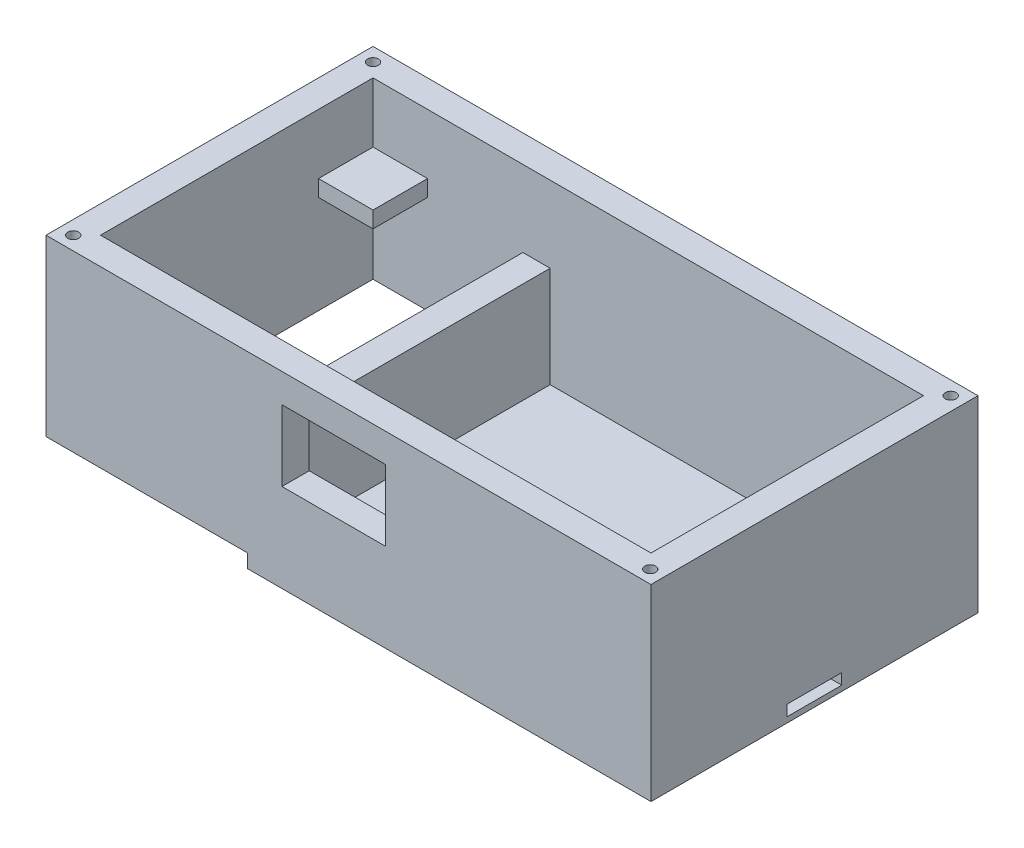
SolidWorks part; units mm, degrees
ref_plane "Front Plane" through (0, 0, 0) normal (0, 0, 1) x (1, 0, 0)
ref_plane "Top Plane" through (0, 0, 0) normal (0, 1, 0) x (1, 0, 0)
ref_plane "Right Plane" through (0, 0, 0) normal (1, 0, 0) x (0, 0, -1)
sketch "Sketch1" plane through (0, 0, 0) normal (0, 1, 0) x (1, 0, 0)
  line L1 (0, 0) -> (111, 0)
  line L2 (0, 0) -> (0, 60)
  line L3 (0, 60) -> (111, 60)
  line L4 (111, 0) -> (111, 60)
  dimension "D1" = 111
  dimension "D2" = 60
extrude "Boss-Extrude1" add sketch "Sketch1" along normal blind 34.5
sketch "Sketch2" plane through (0, 34.5, 0) normal (0, 1, 0) x (1, 0, 0)
  line L0 (55.5, 60) -> (55.5, 0) construction
  line L1 (111, 60) -> (0, 60) construction
  line L2 (0, 0) -> (111, 0) construction
  line L3 (0, 30) -> (111, 30) construction
  line L4 (0, 60) -> (0, 0) construction
  line L5 (111, 0) -> (111, 60) construction
  line L7 (5, 5) -> (106, 5)
  line L8 (5, 5) -> (5, 55)
  line L9 (5, 55) -> (106, 55)
  line L10 (106, 5) -> (106, 55)
  dimension "D1" = 5
  dimension "D2" = 5
  dimension "D3" = 5
  dimension "D4" = 5
  dimension "D5" = 50
  dimension "D6" = 101
extrude "Cut-Extrude1" cut sketch "Sketch2" against normal blind 11
sketch "Sketch3" plane through (0, 34.5, 0) normal (0, 1, 0) x (1, 0, 0)
  line L0 (5, 45) -> (15, 45)
  line L1 (5, 55) -> (5, 5) construction
  line L2 (15, 45) -> (15, 55)
  line L3 (106, 55) -> (5, 55) construction
  line L4 (15, 55) -> (96, 55)
  line L5 (96, 55) -> (96, 45)
  line L6 (96, 45) -> (106, 45)
  line L7 (106, 5) -> (106, 55) construction
  line L8 (106, 45) -> (106, 15)
  line L9 (106, 5) -> (106, 55) construction
  line L10 (106, 15) -> (96, 15)
  line L11 (96, 15) -> (96, 5)
  line L12 (5, 5) -> (106, 5) construction
  line L13 (96, 5) -> (15, 5)
  line L14 (15, 5) -> (15, 15)
  line L15 (15, 15) -> (5, 15)
  line L16 (5, 55) -> (5, 5) construction
  line L17 (5, 15) -> (5, 45)
  dimension "D1" = 10
  dimension "D2" = 10
  dimension "D3" = 10
  dimension "D4" = 10
  dimension "D5" = 10
  dimension "D6" = 10
  dimension "D7" = 10
  dimension "D8" = 10
extrude "Cut-Extrude3" cut sketch "Sketch3" against normal blind 14
sketch "Sketch5" plane through (0, 0, 0) normal (0, -1, 0) x (1, 0, 0)
  line L1 (5, -5) -> (32.5, -5)
  line L2 (5, -5) -> (5, -55)
  line L3 (5, -55) -> (32.5, -55)
  line L4 (32.5, -5) -> (32.5, -55)
  line L6 (0, 0) -> (111, 0) construction
  line L7 (0, -60) -> (0, 0) construction
  line L14 (111, 0) -> (111, -60) construction
  line L15 (106, -55) -> (37.5, -55)
  line L16 (106, -55) -> (106, -5)
  line L17 (106, -5) -> (37.5, -5)
  line L18 (37.5, -55) -> (37.5, -5)
  line L19 (111, -60) -> (0, -60) construction
  dimension "D1" = 27.5
  dimension "D2" = 50
  dimension "D3" = 5
  dimension "D4" = 5
  dimension "D5" = 5
  dimension "D6" = 5
  dimension "D7" = 5
  dimension "D8" = 5
  dimension "D9" = 5
extrude "Cut-Extrude5" cut sketch "Sketch5" against normal blind 18.5 from offset 2 offset against normal yes
sketch "Sketch6" plane through (0, 0, 0) normal (0, -1, 0) x (1, 0, 0)
  line L0 (0, 0) -> (111, 0) construction
  line L1 (0, -60) -> (37, -60)
  line L2 (0, -60) -> (0, 0)
  line L3 (0, 0) -> (37, 0)
  line L4 (37, -60) -> (37, 0)
  dimension "D1" = 60
  dimension "D2" = 37
extrude "Cut-Extrude6" cut sketch "Sketch6" against normal blind 2.5
sketch "Sketch7" plane through (0, 2.5, 0) normal (0, -1, 0) x (-1, 0, 0)
  line L0 (-37, 0) -> (0, 0) construction
  line L1 (0, 0) -> (0, 60) construction
  line L2 (0, 60) -> (-37, 60) construction
  line L3 (-37, 60) -> (-37, 0) construction
  line L4 (-37, 60) -> (-37, 0) construction
  circle A0 centre (-2.5, 57.5) radius 1
  circle A1 centre (-34.5, 57.5) radius 1
  circle A2 centre (-34.5, 2.5) radius 1
  circle A3 centre (-2.5, 2.5) radius 1
  dimension "D1" = 2
  dimension "D2" = 2
  dimension "D3" = 2
  dimension "D4" = 2
  dimension "D5" = 2.5
  dimension "D6" = 2.5
  dimension "D7" = 2.5
  dimension "D8" = 2.5
  dimension "D9" = 2.5
  dimension "D10" = 2.5
  dimension "D11" = 2.5
  dimension "D12" = 2.5
extrude "Cut-Extrude7" cut sketch "Sketch7" against normal blind 4
sketch "Sketch8" plane through (0, 34.5, 0) normal (0, 1, 0) x (1, 0, 0)
  line L0 (111, 60) -> (0, 60) construction
  line L1 (111, 0) -> (111, 60) construction
  line L2 (0, 60) -> (0, 0) construction
  line L3 (0, 0) -> (111, 0) construction
  circle A0 centre (2.5, 57.5) radius 1
  circle A1 centre (108.5, 57.5) radius 1
  circle A2 centre (108.5, 2.3604) radius 1
  circle A3 centre (2.5, 2.5) radius 1
  dimension "D8" = 2
  dimension "D9" = 2
  dimension "D10" = 2
  dimension "D12" = 2
  dimension "D1" = 2.5
  dimension "D2" = 2.5
  dimension "D3" = 2.5
  dimension "D4" = 2.5
  dimension "D5" = 2.5
  dimension "D6" = 2.5
  dimension "D7" = 2.5
  dimension "D11" = 2.5
extrude "Cut-Extrude8" cut sketch "Sketch8" against normal blind 4
sketch "Sketch9" plane through (0, 0, 0) normal (0, 0, 1) x (1, 0, 0)
  line L1 (43.2925, 16.2135) -> (62.2925, 16.2135)
  line L2 (43.2925, 16.2135) -> (43.2925, 29.2135)
  line L3 (43.2925, 29.2135) -> (62.2925, 29.2135)
  line L4 (62.2925, 16.2135) -> (62.2925, 29.2135)
  dimension "D1" = 13
  dimension "D2" = 19
extrude "Cut-Extrude9" cut sketch "Sketch9" against normal blind 10
sketch "Sketch10" plane through (111, 0, 0) normal (1, 0, 0) x (0, 0, -1)
  line L1 (0, 0) -> (60, 0) construction
  line L4 (35, 3) -> (25, 3)
  line L5 (35, 3) -> (35, 1)
  line L6 (35, 1) -> (25, 1)
  line L7 (25, 3) -> (25, 1)
  dimension "D1" = 2
  dimension "D2" = 1
  dimension "D3" = 10
extrude "Cut-Extrude10" cut sketch "Sketch10" against normal blind 70
sketch "Sketch11" plane through (0, 1, 0) normal (0, 1, 0) x (1, 0, 0)
  line L0 (41, 35) -> (106, 35) construction
  line L1 (41, 35) -> (43, 35)
  line L2 (41, 35) -> (41, 25)
  line L3 (41, 25) -> (43, 25)
  line L4 (43, 35) -> (43, 25)
  line L5 (41, 25) -> (41, 35) construction
  dimension "D1" = 2
  dimension "D2" = 10
  dimension "D3" = 0
  dimension "D4" = 0
  dimension "D5" = 2
extrude "Cut-Extrude11" cut sketch "Sketch11" against normal through all
